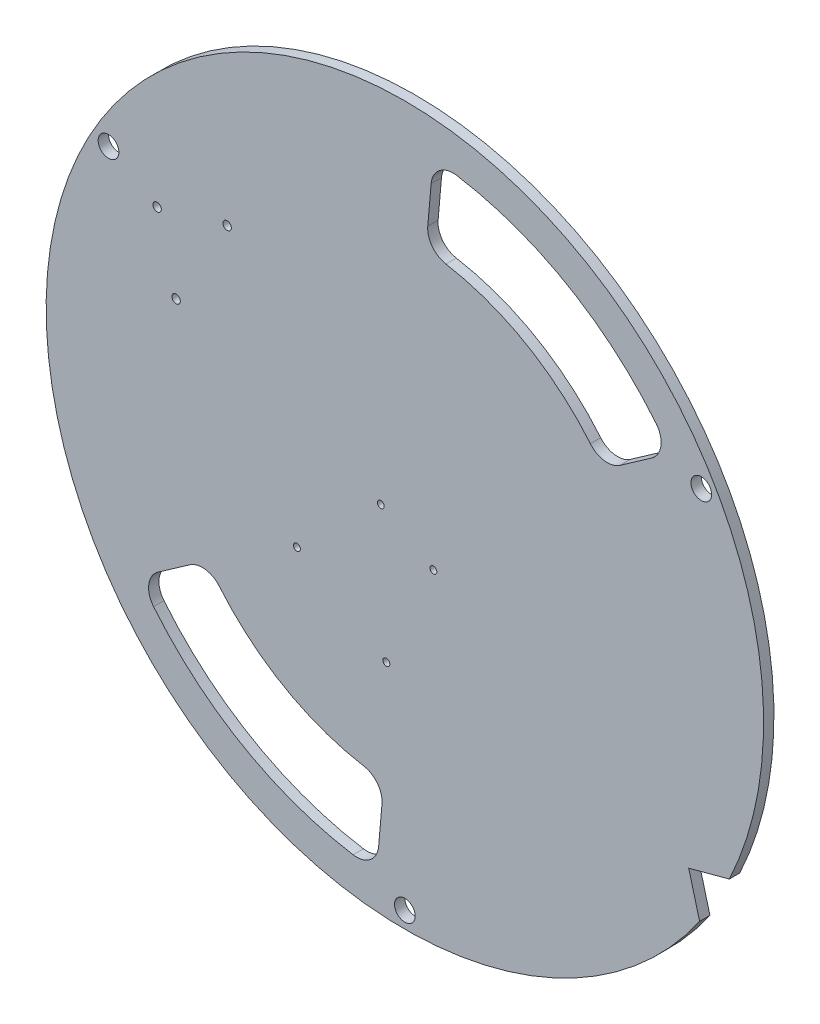
SolidWorks part; units mm, degrees
material "Acrylic (Medium-high impact)"
ref_plane "Front Plane" through (0, 0, 0) normal (0, 0, 1) x (1, 0, 0)
ref_plane "Top Plane" through (0, 0, 0) normal (0, 1, 0) x (1, 0, 0)
ref_plane "Right Plane" through (0, 0, 0) normal (1, 0, 0) x (0, 0, -1)
sketch "Sketch1" plane through (0, 0, 0) normal (0, 0, 1) x (1, 0, 0)
  line L0 (0, 0) -> (0, 139.7) construction
  line L1 (0, 0) -> (157.5, 0) construction
  line L2 (0, 0) -> (78.75, 136.399) construction
  line L3 (9.525, 0) -> (9.525, 157.5) construction
  line L4 (0, 0) -> (142.9808, -82.55) construction
  line L5 (130.6322, -75.4205) -> (135.6432, -94.1219)
  line L7 (130.6322, -75.4205) -> (149.3336, -70.4095)
  line L12 (0, 0) -> (0, -157.5) construction
  line L13 (0, 0) -> (-75.8569, -131.3881) construction
  line L20 (-75.8569, -131.3881) -> (-82.55, -142.9808) construction
  arc A0 (-76.0295, -146.5521) -> (135.6432, -94.1219) centre (0, 0) ccw
  circle A1 centre (-136.399, 78.75) radius 4.7625
  circle A2 centre (0, 0) radius 114.3 construction
  circle A3 centre (0, 0) radius 88.9 construction
  circle A4 centre (0, -157.5) radius 4.7625
  circle A5 centre (136.399, 78.75) radius 4.7625
  arc A6 (149.3336, -70.4095) -> (-88.9031, -139.1195) centre (0, 0) ccw
  arc A7 (-88.9031, -139.1195) -> (-76.0295, -146.5521) centre (0, 0) ccw
  arc A8 (139.7, 0) -> (69.85, 120.9837) centre (0, 0) ccw construction
  arc A9 (9.525, 139.3749) -> (0, 139.7) centre (0, 0) ccw construction
  circle A11 centre (0, 0) radius 148.3041 construction
  arc A35 (-69.85, -120.9837) -> (0, -139.7) centre (0, 0) ccw construction
  circle A36 centre (-57.15, -98.9867) radius 4.7625 construction
  circle A37 centre (-72.7967, -88.12) radius 4.7625 construction
  circle A38 centre (-39.9158, -107.1038) radius 4.7625 construction
  arc A57 (-75.8569, -131.3881) -> (131.8211, -75.102) centre (0, 0) ccw construction
  point P17 (9.525, 148.9207)
  point P18 (0, 0)
  point P20 (9.525, 88.3883)
  point P31 (-125.4647, -61.4386)
  point P122 (0, 0)
  point P151 (0, 0)
  dimension "D2" = 330.2
  dimension "D3" = 9.525
  dimension "D7" = 9.525
  dimension "D4" = 50.8
  dimension "D11" = 60
  dimension "D5" = 45
  dimension "D6" = 45
  dimension "D8" = 3
extrude "Boss-Extrude1" add sketch "Sketch1" along normal blind 4.762
sketch "Sketch5" plane through (0, 0, 4.762) normal (0, 0, 1) x (1, 0, 0)
  line L0 (-81.7197, 74.4573) -> (-105.3758, 33.4838) construction
  line L4 (-113.0906, 67.3654) -> (-114.9513, 64.1425) construction
  line L15 (-93.5307, 54) -> (-73.1064, 42.1319) construction
  circle A0 centre (-114.0209, 65.7539) radius 1.9304
  circle A1 centre (-81.7768, 74.4902) radius 1.9304
  circle A2 centre (-73.0405, 42.2461) radius 1.9304 [skipped]
  circle A3 centre (-105.2847, 33.5098) radius 1.9304
  circle A5 centre (-93.5307, 54) radius 23.6901 construction
  point P20 (-93.5307, 54)
  dimension "D1" = 4
  dimension "D2" = 3.8608
extrude "motor_mounting_holes" cut sketch "Sketch5" against normal through all
sketch "Sketch6" plane through (0, 0, 4.762) normal (0, 0, 1) x (1, 0, 0)
  line L2 (130.6322, -75.4205) -> (0, 0) construction
  circle A0 centre (0, 0) radius 16.0299
sketch "Sketch7" plane through (0, 0, 0) normal (0, 0, -1) x (-1, 0, 0)
  line L2 (-149.3336, -70.4095) -> (-130.6322, -75.4205)
  line L3 (-149.3336, -70.4095) -> (-130.6322, -75.4205)
  line L4 (-130.6322, -75.4205) -> (-135.6432, -94.1219)
  line L5 (-130.6322, -75.4205) -> (-135.6432, -94.1219)
  line L16 (11.9028, -69.3843) -> (54.0492, -45.0511)
  line L17 (7.9932, -68.7086) -> (11.9028, -69.3843)
  line L18 (-18.626, -22.6028) -> (7.9932, -68.7086)
  line L19 (-20.9628, -18.5553) -> (-18.7276, -22.4268)
  line L20 (-10.4922, -12.5101) -> (-20.9628, -18.5553)
  line L21 (-13.1479, -7.7072) -> (-10.455, -12.3714)
  line L22 (15.5015, 2.6146) -> (13.0626, 6.8388)
  line L23 (26.9907, 9.1307) -> (15.6403, 2.5775)
  line L24 (29.4799, 4.8192) -> (26.9907, 9.1307)
  line L25 (56.4547, -41.9025) -> (29.5815, 4.6433)
  line L26 (55.8969, -43.9843) -> (56.4547, -41.9025)
  line L27 (54.2252, -44.9495) -> (55.8969, -43.9843)
  line L28 (11.9028, -69.3843) -> (54.0492, -45.0511) construction
  line L29 (7.9932, -68.7086) -> (11.9028, -69.3843)
  line L30 (-18.626, -22.6028) -> (7.9932, -68.7086) construction
  line L31 (-20.9628, -18.5553) -> (-18.7276, -22.4268) construction
  line L32 (-10.4922, -12.5101) -> (-20.9628, -18.5553) construction
  line L33 (-13.1479, -7.7072) -> (-10.455, -12.3714) construction
  line L34 (15.5015, 2.6146) -> (13.0626, 6.8388) construction
  line L35 (26.9907, 9.1307) -> (15.6403, 2.5775) construction
  line L36 (29.4799, 4.8192) -> (26.9907, 9.1307) construction
  line L37 (56.4547, -41.9025) -> (29.5815, 4.6433) construction
  line L38 (55.8969, -43.9843) -> (56.4547, -41.9025) construction
  line L39 (54.2252, -44.9495) -> (55.8969, -43.9843) construction
  arc A1 (-135.6432, -94.1219) -> (-149.3336, -70.4095) centre (0, 0) ccw
  arc A2 (-135.6432, -94.1219) -> (-149.3336, -70.4095) centre (0, 0) ccw
  circle A3 centre (11.0825, -1.3074) radius 1.5875
  circle A4 centre (11.0825, -1.3074) radius 1.5875
  circle A5 centre (-13.1143, -15.2774) radius 1.5875
  circle A6 centre (-13.1143, -15.2774) radius 1.5875
  circle A7 centre (49.6807, -37.6815) radius 1.5875
  circle A8 centre (49.6807, -37.6815) radius 1.5875
  circle A9 centre (8.5213, -62.9114) radius 1.5875
  arc A10 (-18.626, -22.6028) -> (-18.7276, -22.4268) centre (-18.6768, -22.5148) ccw
  arc A11 (-10.4922, -12.5101) -> (-10.455, -12.3714) centre (-10.4042, -12.4593) ccw
  arc A12 (-13.1479, -7.7072) -> (-13.2476, -7.5302) centre (-13.1986, -7.6192) ccw
  arc A13 (12.9623, 7.0155) -> (-13.2476, -7.5302) centre (-0.093, -0.347) ccw
  arc A14 (12.9623, 7.0155) -> (13.0626, 6.8388) centre (13.0119, 6.9268) ccw
  arc A15 (15.5015, 2.6146) -> (15.6403, 2.5775) centre (15.5523, 2.5267) ccw
  arc A16 (29.4799, 4.8192) -> (29.5815, 4.6433) centre (29.5307, 4.7312) ccw
  arc A17 (54.2252, -44.9495) -> (54.0492, -45.0511) centre (54.1372, -45.0003) ccw
  arc A18 (-18.626, -22.6028) -> (-18.7276, -22.4268) centre (-18.6768, -22.5148) ccw construction
  arc A19 (-10.4922, -12.5101) -> (-10.455, -12.3714) centre (-10.4042, -12.4593) ccw construction
  arc A20 (-13.1479, -7.7072) -> (-13.2476, -7.5302) centre (-13.1986, -7.6192) ccw construction
  arc A21 (12.9623, 7.0155) -> (-13.2476, -7.5302) centre (-0.093, -0.347) ccw construction
  arc A22 (12.9623, 7.0155) -> (13.0626, 6.8388) centre (13.0119, 6.9268) ccw construction
  arc A23 (15.5015, 2.6146) -> (15.6403, 2.5775) centre (15.5523, 2.5267) ccw construction
  arc A24 (29.4799, 4.8192) -> (29.5815, 4.6433) centre (29.5307, 4.7312) ccw construction
  arc A25 (54.2252, -44.9495) -> (54.0492, -45.0511) centre (54.1372, -45.0003) ccw construction
  circle A26 centre (8.5213, -62.9114) radius 1.5875
  dimension "D1" = 0
  dimension "D2" = 0
  dimension "D3" = 0
  dimension "D4" = 0
  dimension "D5" = 0
  dimension "D6" = 0
extrude "arduino mounting holes" cut sketch "Sketch7" against normal through all contours A6 | A26 | A4 | A8
sketch "Sketch8" plane through (0, 0, 4.762) normal (0, 0, 1) x (1, 0, 0)
  line L0 (0, 0) -> (130.6322, -75.4205) construction
  line L1 (0, 0) -> (74.6125, 129.2326) construction
  line L2 (12.0879, 138.1656) -> (10.5335, 120.3988)
  line L3 (113.611, 79.5512) -> (99.0017, 69.3217)
  line L4 (-113.611, -79.5512) -> (-99.0017, -69.3217)
  line L5 (-12.0879, -138.1656) -> (-10.5335, -120.3988)
  arc A0 (115.658, 94.2938) -> (23.8319, 147.3097) centre (0, 0) ccw
  arc A1 (149.3336, -70.4095) -> (135.6432, -94.1219) centre (0, 0) ccw construction
  arc A2 (85.369, 71.1401) -> (18.9246, 109.5017) centre (0, 0) ccw
  arc A3 (113.611, 79.5512) -> (115.658, 94.2938) centre (107.7834, 87.8738) ccw
  arc A4 (99.0017, 69.3217) -> (85.369, 71.1401) centre (93.1741, 77.6443) cw
  arc A5 (10.5335, 120.3988) -> (18.9246, 109.5017) centre (20.6549, 119.5133) ccw
  arc A6 (12.0879, 138.1656) -> (23.8319, 147.3097) centre (22.2093, 137.2801) cw
  arc A7 (-99.0017, -69.3217) -> (-85.369, -71.1401) centre (-93.1741, -77.6443) cw
  arc A8 (-113.611, -79.5512) -> (-115.658, -94.2938) centre (-107.7834, -87.8738) ccw
  arc A9 (-23.8319, -147.3097) -> (-115.658, -94.2938) centre (0, 0) cw
  arc A10 (-12.0879, -138.1656) -> (-23.8319, -147.3097) centre (-22.2093, -137.2801) cw
  arc A11 (-10.5335, -120.3988) -> (-18.9246, -109.5017) centre (-20.6549, -119.5133) ccw
  arc A12 (-18.9246, -109.5017) -> (-85.369, -71.1401) centre (0, 0) cw
  point P14 (122.238, 85.5919)
  point P17 (91.0283, 63.7387)
  point P20 (9.6852, 110.7021)
  point P23 (13.0058, 148.6572)
  dimension "D1" = 15.875
  dimension "D2" = 38.1
  dimension "D3" = 90
  dimension "D5" = 10.16
  dimension "D4" = 25
extrude "handles" cut sketch "Sketch8" against normal through all
equation "\"D6@Sketch1\"=\"D5@Sketch1\""
